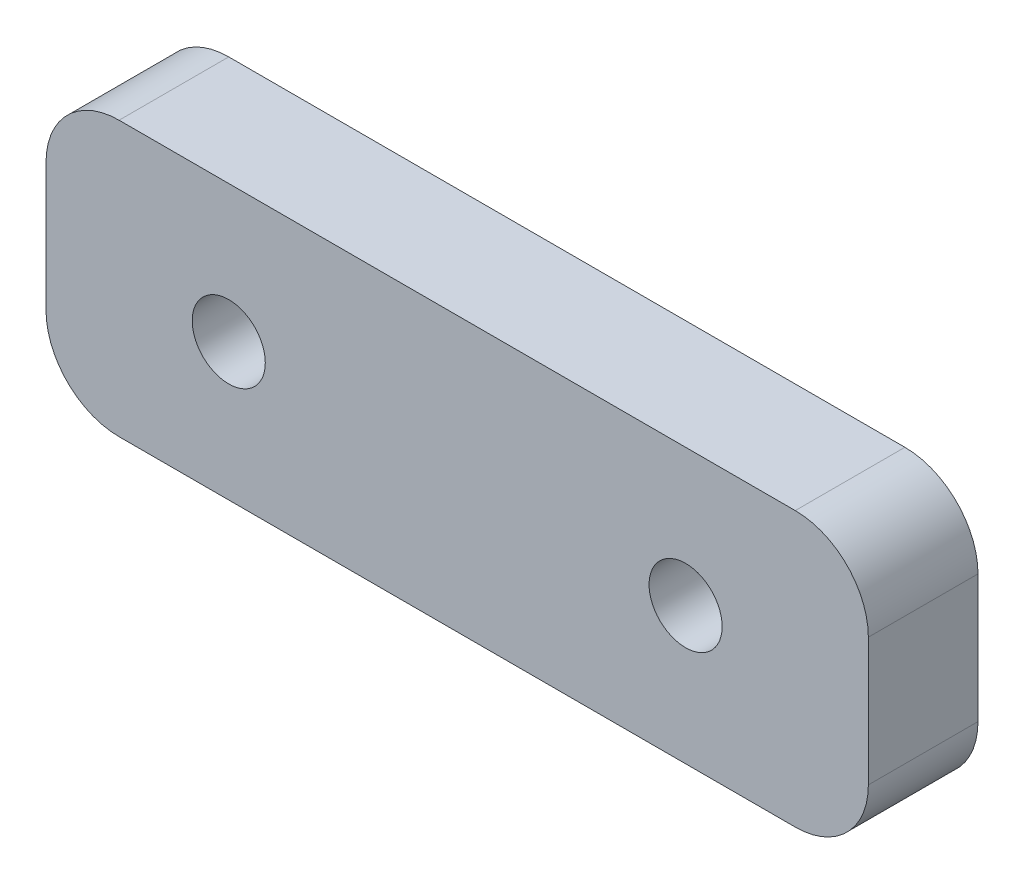
SolidWorks part; units mm, degrees
material "Beech"
ref_plane "Front Plane" through (0, 0, 0) normal (0, 0, 1) x (1, 0, 0)
ref_plane "Top Plane" through (0, 0, 0) normal (0, 1, 0) x (1, 0, 0)
ref_plane "Right Plane" through (0, 0, 0) normal (1, 0, 0) x (0, 0, -1)
sketch "Sketch1" plane through (0, 0, 0) normal (0, 0, 1) x (1, 0, 0)
  line L0 (0, 0) -> (25, 0) construction
  line L2 (-10, -7.5) -> (35, -7.5)
  line L3 (-10, -7.5) -> (-10, 7.5)
  line L4 (-10, 7.5) -> (35, 7.5)
  line L5 (35, -7.5) -> (35, 7.5)
  circle A0 centre (0, 0) radius 2
  circle A1 centre (25, 0) radius 2
  point P9 (-10, 0)
  dimension "D1" = 4
  dimension "D2" = 25
  dimension "D3" = 15
  dimension "D4" = 10
  dimension "D5" = 10
extrude "Boss-Extrude1" add sketch "Sketch1" along normal blind 6
fillet "Fillet1" radius 4 4 edges at (-10, 7.5, 3) (35, -7.5, 3) (-10, -7.5, 3) (35, 7.5, 3)
